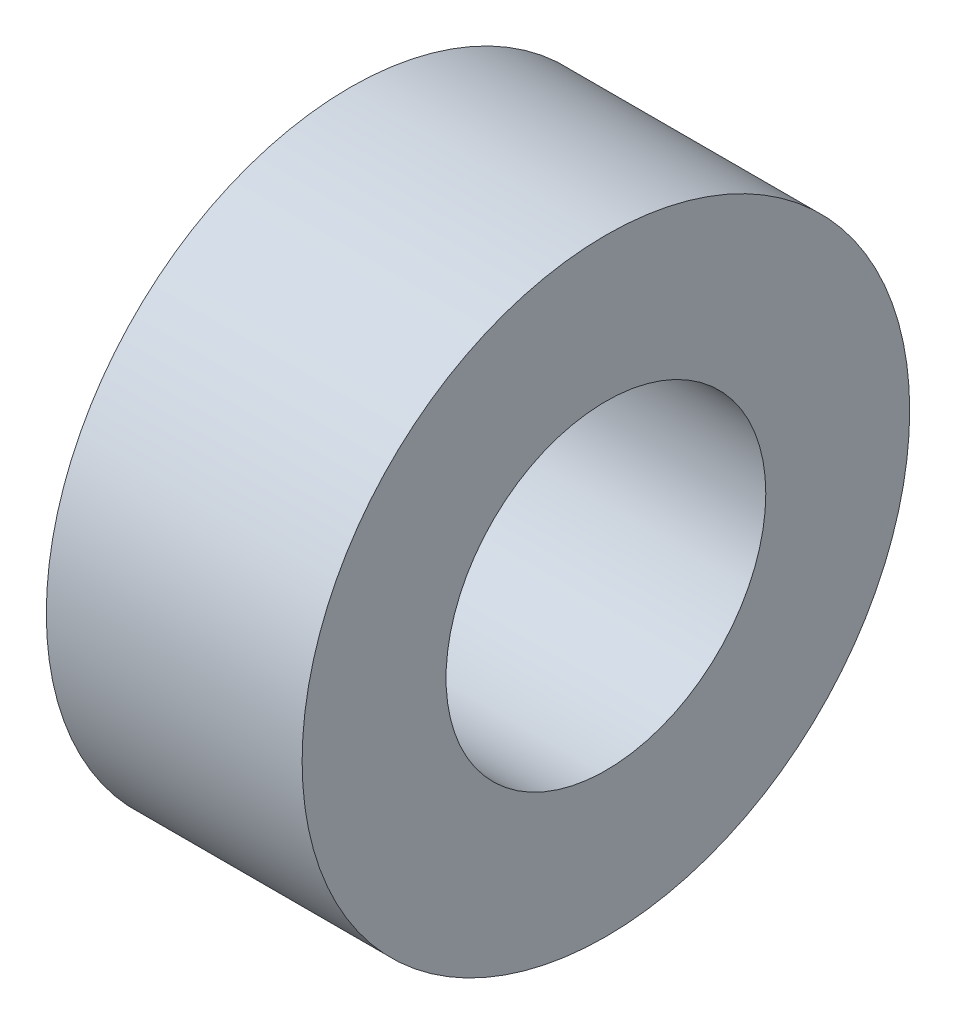
SolidWorks part; units mm, degrees
ref_plane "Front Plane" through (0, 0, 0) normal (0, 0, 1) x (1, 0, 0)
ref_plane "Top Plane" through (0, 0, 0) normal (0, 1, 0) x (1, 0, 0)
ref_plane "Right Plane" through (0, 0, 0) normal (1, 0, 0) x (0, 0, -1)
sketch "Sketch1" plane through (0, 0, 0) normal (1, 0, 0) x (0, 0, -1)
  circle A0 centre (0, 0) radius 9.5
  circle A1 centre (0, 0) radius 5
  dimension "D1" = 10
  dimension "D2" = 19
extrude "Boss-Extrude1" add sketch "Sketch1" along normal blind 8
